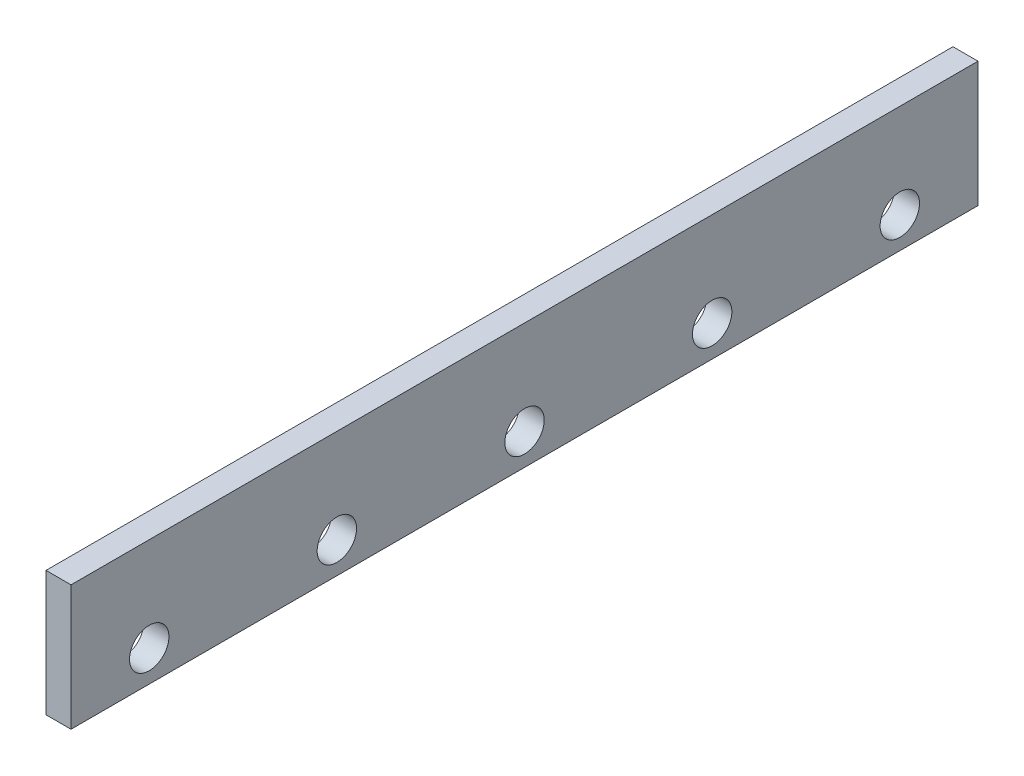
SolidWorks part; units mm, degrees
ref_plane "Alzado" through (0, 0, 0) normal (0, 0, 1) x (1, 0, 0)
ref_plane "Planta" through (0, 0, 0) normal (0, 1, 0) x (1, 0, 0)
ref_plane "Vista lateral" through (0, 0, 0) normal (1, 0, 0) x (0, 0, -1)
sketch "Croquis1" plane through (0, 0, 0) normal (1, 0, 0) x (0, 0, -1)
  line L0 (0, 0) -> (580, 0)
  line L1 (580, 0) -> (580, 80)
  line L2 (0, 0) -> (0, 80)
  line L3 (0, 80) -> (580, 80)
  line L4 (50, 20) -> (170, 20) construction
  circle A0 centre (50, 20) radius 12.6
  circle A1 centre (170, 20) radius 12.6
  circle A2 centre (290, 20) radius 12.6
  circle A3 centre (410, 20) radius 12.6
  circle A4 centre (530, 20) radius 12.6
  dimension "D5" = 25.2
  dimension "D1" = 580
  dimension "D2" = 80
  dimension "D3" = 50
  dimension "D4" = 20
  dimension "D7" = 120
  dimension "D6" = 5
extrude "Saliente-Extruir1" add sketch "Croquis1" along normal blind 16
